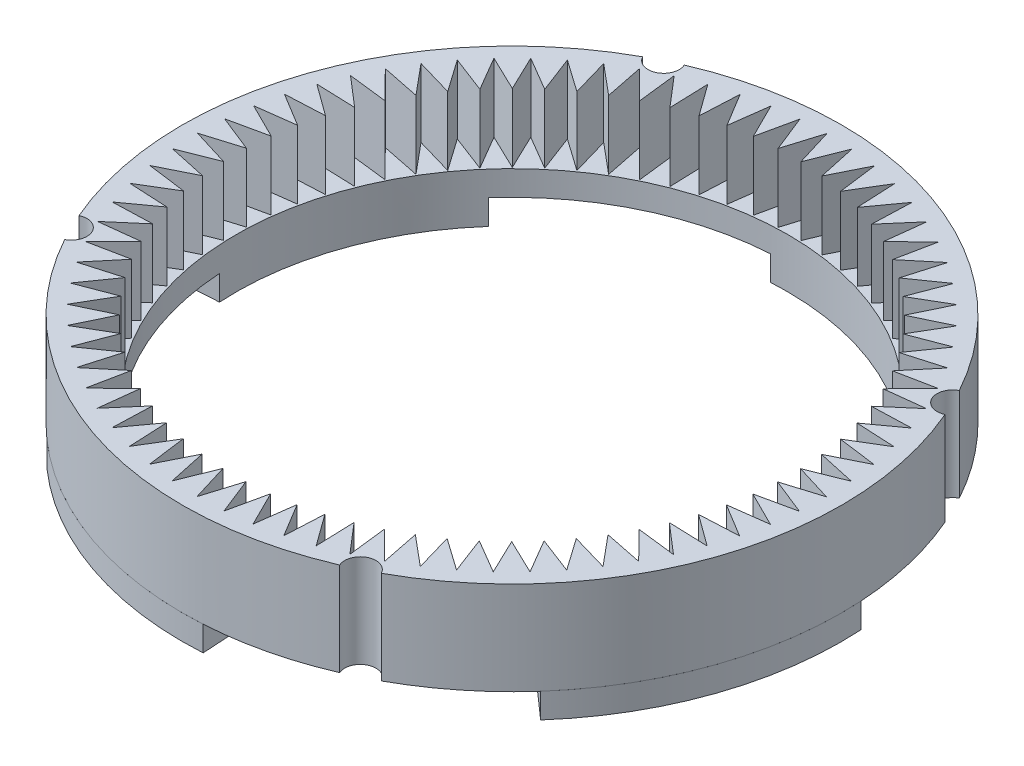
SolidWorks part; units mm, degrees
ref_plane "Front Plane" through (0, 0, 0) normal (0, 0, 1) x (1, 0, 0)
ref_plane "Top Plane" through (0, 0, 0) normal (0, 1, 0) x (1, 0, 0)
ref_plane "Right Plane" through (0, 0, 0) normal (1, 0, 0) x (0, 0, -1)
sketch "Sketch1" plane through (0, 0, 0) normal (0, 1, 0) x (1, 0, 0)
  circle A1 centre (0, 0) radius 23
extrude "Boss-Extrude1" add sketch "Sketch1" against normal blind 2
sketch "Sketch2" plane through (0, 0, 0) normal (0, 1, 0) x (1, 0, 0)
  circle A0 centre (0, 0) radius 30
  circle A1 centre (0, 0) radius 22.2
extrude "Boss-Extrude2" add sketch "Sketch2" along normal blind 11
sketch "Sketch3" plane through (0, 0, 0) normal (0, 1, 0) x (1, 0, 0)
  circle A0 centre (0, 0) radius 11.25
extrude "Cut-Extrude1" cut sketch "Sketch3" against normal blind 10 contours A0
ref_plane "Plane1" through (0, 11, 0) normal (0, 1, 0) x (1, 0, 0)
ref_plane "Plane2" through (0, -2, 0) normal (0, -1, 0) x (-1, 0, 0)
ref_plane "Plane3" through (0, 0, 0) normal (0, -1, 0) x (-1, 0, 0)
sketch "Sketch6" plane through (0, 0, 0) normal (1, 0, 0) x (0, 0, -1)
  line L0 (29.6174, 10.3701) -> (30.176, 10.3701)
  line L1 (30.176, 10.3701) -> (30.176, 0.8441)
  line L2 (30.176, 5.6071) -> (35.5665, 5.6071) construction
  line L3 (30.176, 0.8441) -> (29.6174, 0.8441)
  line L4 (28.5358, 8.7702) -> (28.5358, 8.4631)
  line L5 (28.5358, 7.1702) -> (28.5358, 6.8631)
  line L6 (28.5358, 5.5702) -> (28.5358, 5.2631)
  line L7 (28.5358, 3.9702) -> (28.5358, 3.6631)
  line L8 (28.5358, 2.3702) -> (28.5358, 2.0631)
  line L9 (28.5358, 9.1511) -> (28.5358, 8.7702)
  arc A0 (28.5358, 9.1511) -> (29.6174, 10.3701) centre (29.7636, 9.1511) cw
  arc A1 (28.5358, 8.4631) -> (28.5358, 7.1702) centre (28.9161, 7.8166) ccw
  arc A2 (28.5358, 6.8631) -> (28.5358, 5.5702) centre (28.9161, 6.2166) ccw
  arc A3 (28.5358, 5.2631) -> (28.5358, 3.9702) centre (28.9161, 4.6166) ccw
  arc A4 (28.5358, 3.6631) -> (28.5358, 2.3702) centre (28.9161, 3.0166) ccw
  arc A5 (28.5358, 2.0631) -> (29.6174, 0.8441) centre (29.7636, 2.0631) ccw
  dimension "D2" = 1.6
  dimension "D3" = 1.6
  dimension "D4" = 1.6
ref_axis "Axis1" through (0, -2, 0) along (0, 1, 0)
sketch "Sketch10" plane through (0, 11, 0) normal (0, 1, 0) x (1, 0, 0)
  line L0 (8.2003, -23.949) -> (8.0956, -20.7964)
  line L1 (8.2003, -23.949) -> (7.2077, -21.0502) construction
  line L2 (8.2003, -23.949) -> (6.3506, -21.3939)
  line L3 (6.1946, -24.5444) -> (6.3506, -21.3939)
  line L5 (6.1946, -24.5444) -> (4.5623, -21.8453)
  line L6 (4.1466, -24.9721) -> (4.5623, -21.8453)
  line L7 (4.1466, -24.9721) -> (2.7427, -22.1474)
  line L8 (2.0703, -25.2292) -> (2.7427, -22.1474)
  line L9 (2.0703, -25.2292) -> (0.9044, -22.2983)
  line L10 (-0.0202, -25.314) -> (0.9044, -22.2983)
  line L11 (-0.0202, -25.314) -> (-0.9401, -22.2968)
  line L12 (-2.1106, -25.2259) -> (-0.9401, -22.2968)
  line L13 (-2.1106, -25.2259) -> (-2.7781, -22.143)
  line L14 (-4.1865, -24.9654) -> (-2.7781, -22.143)
  line L15 (-4.1865, -24.9654) -> (-4.5972, -21.838)
  line L16 (-6.2338, -24.5345) -> (-4.5972, -21.838)
  line L17 (-6.2338, -24.5345) -> (-6.3848, -21.3837)
  line L18 (-8.2386, -23.9359) -> (-6.3848, -21.3837)
  line L19 (-8.2386, -23.9359) -> (-8.1289, -20.7835)
  line L20 (-10.1871, -23.1738) -> (-8.1289, -20.7835)
  line L21 (-10.1871, -23.1738) -> (-9.8174, -20.0412)
  line L22 (-12.0659, -22.2534) -> (-9.8174, -20.0412)
  line L23 (-12.0659, -22.2534) -> (-11.4389, -19.162)
  line L24 (-13.8624, -21.181) -> (-11.4389, -19.162)
  line L25 (-13.8624, -21.181) -> (-12.9822, -18.152)
  line L26 (-15.5642, -19.9639) -> (-12.9822, -18.152)
  line L27 (-15.5642, -19.9639) -> (-14.4368, -17.0179)
  line L28 (-17.1596, -18.6104) -> (-14.4368, -17.0179)
  line L29 (-17.1596, -18.6104) -> (-15.7928, -15.7676)
  line L30 (-18.6378, -17.1298) -> (-15.7928, -15.7676)
  line L31 (-18.6378, -17.1298) -> (-17.041, -14.4096)
  line L32 (-19.9887, -15.5322) -> (-17.041, -14.4096)
  line L33 (-19.9887, -15.5322) -> (-18.1727, -12.9531)
  line L34 (-21.2031, -13.8285) -> (-18.1727, -12.9531)
  line L35 (-21.2031, -13.8285) -> (-19.1803, -11.4082)
  line L36 (-22.2726, -12.0304) -> (-19.1803, -11.4082)
  line L37 (-22.2726, -12.0304) -> (-20.0569, -9.7854)
  line L38 (-23.19, -10.15) -> (-20.0569, -9.7854)
  line L39 (-23.19, -10.15) -> (-20.7964, -8.0956)
  line L40 (-23.949, -8.2003) -> (-20.7964, -8.0956)
  line L41 (-23.949, -8.2003) -> (-21.3939, -6.3506)
  line L42 (-24.5444, -6.1946) -> (-21.3939, -6.3506)
  line L43 (-24.5444, -6.1946) -> (-21.8453, -4.5623)
  line L44 (-24.9721, -4.1466) -> (-21.8453, -4.5623)
  line L45 (-24.9721, -4.1466) -> (-22.1474, -2.7427)
  line L46 (-25.2292, -2.0703) -> (-22.1474, -2.7427)
  line L47 (-25.2292, -2.0703) -> (-22.2983, -0.9044)
  line L48 (-25.314, 0.0202) -> (-22.2983, -0.9044)
  line L49 (-25.314, 0.0202) -> (-22.2968, 0.9401)
  line L50 (-25.2259, 2.1106) -> (-22.2968, 0.9401)
  line L51 (-25.2259, 2.1106) -> (-22.143, 2.7781)
  line L52 (-24.9654, 4.1865) -> (-22.143, 2.7781)
  line L53 (-24.9654, 4.1865) -> (-21.838, 4.5972)
  line L54 (-24.5345, 6.2338) -> (-21.838, 4.5972)
  line L55 (-24.5345, 6.2338) -> (-21.3837, 6.3848)
  line L56 (-23.9359, 8.2386) -> (-21.3837, 6.3848)
  line L57 (-23.9359, 8.2386) -> (-20.7835, 8.1289)
  line L58 (-23.1738, 10.1871) -> (-20.7835, 8.1289)
  line L59 (-23.1738, 10.1871) -> (-20.0412, 9.8174)
  line L60 (-22.2534, 12.0659) -> (-20.0412, 9.8174)
  line L61 (-22.2534, 12.0659) -> (-19.162, 11.4389)
  line L62 (-21.181, 13.8624) -> (-19.162, 11.4389)
  line L63 (-21.181, 13.8624) -> (-18.152, 12.9822)
  line L64 (-19.9639, 15.5642) -> (-18.152, 12.9822)
  line L65 (-19.9639, 15.5642) -> (-17.0179, 14.4368)
  line L66 (-18.6104, 17.1596) -> (-17.0179, 14.4368)
  line L67 (-18.6104, 17.1596) -> (-15.7676, 15.7928)
  line L68 (-17.1298, 18.6378) -> (-15.7676, 15.7928)
  line L69 (-17.1298, 18.6378) -> (-14.4096, 17.041)
  line L70 (-15.5322, 19.9887) -> (-14.4096, 17.041)
  line L71 (-15.5322, 19.9887) -> (-12.9531, 18.1727)
  line L72 (-13.8285, 21.2031) -> (-12.9531, 18.1727)
  line L73 (-13.8285, 21.2031) -> (-11.4082, 19.1803)
  line L74 (-12.0304, 22.2726) -> (-11.4082, 19.1803)
  line L75 (-12.0304, 22.2726) -> (-9.7854, 20.0569)
  line L76 (-10.15, 23.19) -> (-9.7854, 20.0569)
  line L77 (-10.15, 23.19) -> (-8.0956, 20.7964)
  line L78 (-8.2003, 23.949) -> (-8.0956, 20.7964)
  line L79 (-8.2003, 23.949) -> (-6.3506, 21.3939)
  line L80 (-6.1946, 24.5444) -> (-6.3506, 21.3939)
  line L81 (-6.1946, 24.5444) -> (-4.5623, 21.8453)
  line L82 (-4.1466, 24.9721) -> (-4.5623, 21.8453)
  line L83 (-4.1466, 24.9721) -> (-2.7427, 22.1474)
  line L84 (-2.0703, 25.2292) -> (-2.7427, 22.1474)
  line L85 (-2.0703, 25.2292) -> (-0.9044, 22.2983)
  line L86 (0.0202, 25.314) -> (-0.9044, 22.2983)
  line L87 (0.0202, 25.314) -> (0.9401, 22.2968)
  line L88 (2.1106, 25.2259) -> (0.9401, 22.2968)
  line L89 (2.1106, 25.2259) -> (2.7781, 22.143)
  line L90 (4.1865, 24.9654) -> (2.7781, 22.143)
  line L91 (4.1865, 24.9654) -> (4.5972, 21.838)
  line L92 (6.2338, 24.5345) -> (4.5972, 21.838)
  line L93 (6.2338, 24.5345) -> (6.3848, 21.3837)
  line L94 (8.2386, 23.9359) -> (6.3848, 21.3837)
  line L95 (8.2386, 23.9359) -> (8.1289, 20.7835)
  line L96 (10.1871, 23.1738) -> (8.1289, 20.7835)
  line L97 (10.1871, 23.1738) -> (9.8174, 20.0412)
  line L98 (12.0659, 22.2534) -> (9.8174, 20.0412)
  line L99 (12.0659, 22.2534) -> (11.4389, 19.162)
  line L100 (13.8624, 21.181) -> (11.4389, 19.162)
  line L101 (13.8624, 21.181) -> (12.9822, 18.152)
  line L102 (15.5642, 19.9639) -> (12.9822, 18.152)
  line L103 (15.5642, 19.9639) -> (14.4368, 17.0179)
  line L104 (17.1596, 18.6104) -> (14.4368, 17.0179)
  line L105 (17.1596, 18.6104) -> (15.7928, 15.7676)
  line L106 (18.6378, 17.1298) -> (15.7928, 15.7676)
  line L107 (18.6378, 17.1298) -> (17.041, 14.4096)
  line L108 (19.9887, 15.5322) -> (17.041, 14.4096)
  line L109 (19.9887, 15.5322) -> (18.1727, 12.9531)
  line L110 (21.2031, 13.8285) -> (18.1727, 12.9531)
  line L111 (21.2031, 13.8285) -> (19.1803, 11.4082)
  line L112 (22.2726, 12.0304) -> (19.1803, 11.4082)
  line L113 (22.2726, 12.0304) -> (20.0569, 9.7854)
  line L114 (23.19, 10.15) -> (20.0569, 9.7854)
  line L115 (23.19, 10.15) -> (20.7964, 8.0956)
  line L116 (23.949, 8.2003) -> (20.7964, 8.0956)
  line L117 (23.949, 8.2003) -> (21.3939, 6.3506)
  line L118 (24.5444, 6.1946) -> (21.3939, 6.3506)
  line L119 (24.5444, 6.1946) -> (21.8453, 4.5623)
  line L120 (24.9721, 4.1466) -> (21.8453, 4.5623)
  line L121 (24.9721, 4.1466) -> (22.1474, 2.7427)
  line L122 (25.2292, 2.0703) -> (22.1474, 2.7427)
  line L123 (25.2292, 2.0703) -> (22.2983, 0.9044)
  line L124 (25.314, -0.0202) -> (22.2983, 0.9044)
  line L125 (25.314, -0.0202) -> (22.2968, -0.9401)
  line L126 (25.2259, -2.1106) -> (22.2968, -0.9401)
  line L127 (25.2259, -2.1106) -> (22.143, -2.7781)
  line L128 (24.9654, -4.1865) -> (22.143, -2.7781)
  line L129 (24.9654, -4.1865) -> (21.838, -4.5972)
  line L130 (24.5345, -6.2338) -> (21.838, -4.5972)
  line L131 (24.5345, -6.2338) -> (21.3837, -6.3848)
  line L132 (23.9359, -8.2386) -> (21.3837, -6.3848)
  line L133 (23.9359, -8.2386) -> (20.7835, -8.1289)
  line L134 (23.1738, -10.1871) -> (20.7835, -8.1289)
  line L135 (23.1738, -10.1871) -> (20.0412, -9.8174)
  line L136 (22.2534, -12.0659) -> (20.0412, -9.8174)
  line L137 (22.2534, -12.0659) -> (19.162, -11.4389)
  line L138 (21.181, -13.8624) -> (19.162, -11.4389)
  line L139 (21.181, -13.8624) -> (18.152, -12.9822)
  line L140 (19.9639, -15.5642) -> (18.152, -12.9822)
  line L141 (19.9639, -15.5642) -> (17.0179, -14.4368)
  line L142 (18.6104, -17.1596) -> (17.0179, -14.4368)
  line L143 (18.6104, -17.1596) -> (15.7676, -15.7928)
  line L144 (17.1298, -18.6378) -> (15.7676, -15.7928)
  line L145 (17.1298, -18.6378) -> (14.4096, -17.041)
  line L146 (15.5322, -19.9887) -> (14.4096, -17.041)
  line L147 (15.5322, -19.9887) -> (12.9531, -18.1727)
  line L148 (13.8285, -21.2031) -> (12.9531, -18.1727)
  line L149 (13.8285, -21.2031) -> (11.4082, -19.1803)
  line L150 (12.0304, -22.2726) -> (11.4082, -19.1803)
  line L151 (12.0304, -22.2726) -> (9.7854, -20.0569)
  line L152 (10.15, -23.19) -> (9.7854, -20.0569)
  line L153 (10.15, -23.19) -> (8.0956, -20.7964)
  line L184 (7.2077, -21.0502) -> (8.5243, -24.8951) construction
  point P235 (0, 0)
  dimension "D1" = 17
extrude "Cut-Extrude8" cut sketch "Sketch10" against normal blind 5.5
sketch "Sketch5" plane through (0, 11, 0) normal (0, 1, 0) x (1, 0, 0)
  line L0 (0, 0) -> (20.0775, 9.7954) construction
  line L1 (20.0775, 9.7954) -> (26.9622, 13.1544) construction
  circle A1 centre (0, 0) radius 30 construction
  circle A2 centre (23.8167, 11.6197) radius 1.25
  circle A3 centre (11.6197, -23.8167) radius 1.25
  circle A5 centre (-23.8167, -11.6197) radius 1.25
  circle A7 centre (-11.6197, 23.8167) radius 1.25
  point P21 (0, 0)
  dimension "D1" = 4
extrude "Cut-Extrude3" cut sketch "Sketch5" against normal through all
sketch "Sketch8" plane through (0, 0, 0) normal (0, -1, 0) x (-1, 0, 0)
  circle A0 centre (-23.8167, 11.6197) radius 2.5
  circle A1 centre (11.6197, 23.8167) radius 2.5
  circle A2 centre (23.8167, -11.6197) radius 2.5
  circle A3 centre (-11.6197, -23.8167) radius 2.5
  point P11 (0, 0)
extrude "Cut-Extrude5" cut sketch "Sketch8" against normal blind 2
ref_plane "Plane4" through (0, 0, 0) normal (0, 1, 0) x (1, 0, 0)
revolve "Cut-Revolve1" cut sketch "Sketch6" angle 360 about axis through (0, -2, 0) along (0, 1, 0)
sketch "Sketch12" plane through (0, -2, 0) normal (0, -1, 0) x (-1, 0, 0)
  line L2 (-19.6103, 3.4061) -> (-22.6044, 3.9868)
  line L3 (-19.1966, 5.5081) -> (-22.0729, 6.2962)
  line L8 (-22.7811, -2.8065) -> (-13.2828, -1.9137)
  line L9 (-19.2445, 12.5101) -> (-11.1512, 7.8264)
  line L11 (-13.2828, -1.9137) -> (-11.1512, 7.8264)
  arc A0 (-19.2445, 12.5101) -> (-22.0729, 6.2962) centre (0, 0) ccw
  arc A1 (-22.6044, 3.9868) -> (-22.7811, -2.8065) centre (0, 0) ccw
  arc A10 (-19.6103, 3.4061) -> (-19.1966, 5.5081) centre (-16.1341, 3.8136) ccw
extrude "Boss-Extrude3" add sketch "Sketch12" along normal blind 3
sketch "Sketch13" plane through (0, -2, 0) normal (0, -1, 0) x (-1, 0, 0)
  circle A0 centre (-16.1341, 3.8136) radius 3.5
extrude "Cut-Extrude9" cut sketch "Sketch13" against normal blind 3 contours A0
ref_plane "Plane5" through (0, 0, 0) normal (0, -1, 0) x (-1, 0, 0)
sketch "Sketch15" plane through (0, 0, 0) normal (0, -1, 0) x (-1, 0, 0)
  line L0 (-27.6851, 4.3056) -> (-29.0627, 4.5727)
  line L1 (-26.7661, 8.2772) -> (-28.1306, 8.6203)
  line L2 (-29.0627, 4.5727) -> (-29.8955, 4.7341)
  line L3 (-28.1306, 8.6203) -> (-29.0951, 8.8628)
  line L4 (-29.0951, 8.8628) -> (-29.8955, 4.7341)
  line L5 (-27.6851, 4.3056) -> (-26.7661, 8.2772)
extrude "Cut-Extrude10" cut sketch "Sketch15" against normal blind 4
sketch "Sketch16" plane through (0, 11, 0) normal (0, 1, 0) x (1, 0, 0)
  circle A0 centre (0, 0) radius 26.5
  circle A1 centre (0, 0) radius 30
extrude "Cut-Extrude13" cut sketch "Sketch16" against normal blind 16
ref_plane "Plane6" through (0, 3.5, 0) normal (0, 1, 0) x (1, 0, 0)
sketch "Sketch17" plane through (0, 3.5, 0) normal (0, 1, 0) x (1, 0, 0)
  circle A0 centre (0, 0) radius 26.9449
  circle A1 centre (0, 0) radius 10.1249
extrude "Cut-Extrude15" cut sketch "Sketch17" against normal blind 16
sketch "Sketch18" plane through (0, 3.5, 0) normal (0, -1, 0) x (1, 0, 0)
  line L0 (-11.6197, -23.8167) -> (11.6197, 23.8167) construction
  line L1 (23.8167, -11.6197) -> (-23.8167, 11.6197) construction
  line L2 (17.5523, -19.8554) -> (14.7026, -16.6335)
  line L3 (26.4521, -1.6135) -> (22.1589, -1.3504)
  line L4 (-1.6285, -26.4512) -> (-1.3654, -22.158)
  line L5 (-19.8454, -17.5635) -> (-16.6236, -14.7138)
  line L6 (-22.158, 1.3654) -> (-26.4512, 1.6285)
  line L7 (16.6335, 14.7026) -> (19.8554, 17.5523)
  line L8 (1.3504, 22.1589) -> (1.6135, 26.4521)
  line L9 (-14.7138, 16.6236) -> (-17.5635, 19.8454)
  arc A0 (26.4521, -1.6135) -> (19.8554, 17.5523) centre (0, 0) ccw
  arc A1 (22.1589, -1.3504) -> (16.6335, 14.7026) centre (0, 0) ccw
  arc A2 (-1.6285, -26.4512) -> (17.5523, -19.8554) centre (0, 0) ccw
  arc A3 (-1.3654, -22.158) -> (14.7026, -16.6335) centre (0, 0) ccw
  arc A4 (-26.4512, 1.6285) -> (-19.8454, -17.5635) centre (0, 0) ccw
  arc A5 (-22.158, 1.3654) -> (-16.6236, -14.7138) centre (0, 0) ccw
  arc A6 (1.6135, 26.4521) -> (-17.5635, 19.8454) centre (0, 0) ccw
  arc A7 (1.3504, 22.1589) -> (-14.7138, 16.6236) centre (0, 0) ccw
  dimension "D1" = 22.5
  dimension "D2" = 22.5
extrude "Boss-Extrude4" add sketch "Sketch18" along normal blind 2
